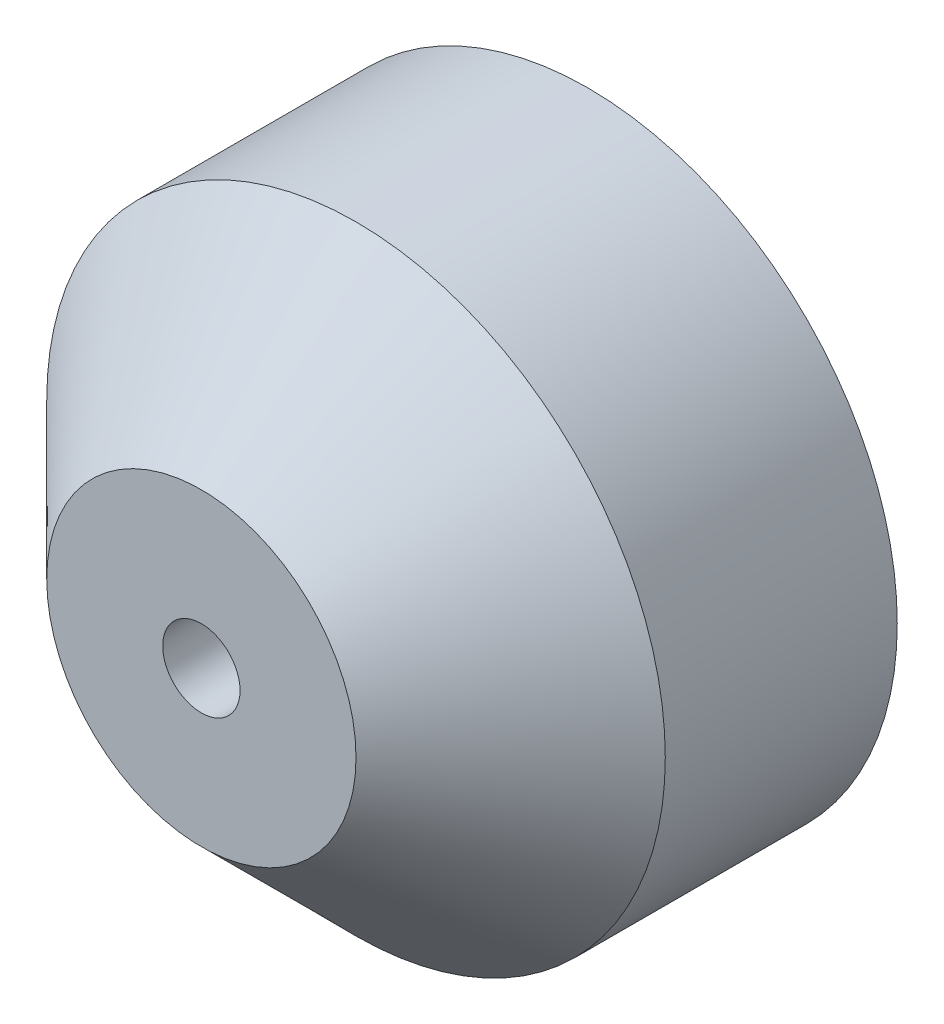
SolidWorks part; units mm, degrees
ref_plane "Front Plane" through (0, 0, 0) normal (0, 0, 1) x (1, 0, 0)
ref_plane "Top Plane" through (0, 0, 0) normal (0, 1, 0) x (1, 0, 0)
ref_plane "Right Plane" through (0, 0, 0) normal (1, 0, 0) x (0, 0, -1)
sketch "Sketch1" plane through (0, 0, 0) normal (0, 0, 1) x (1, 0, 0)
  circle A0 centre (0, 0) radius 20
  dimension "D1" = 40
extrude "Boss-Extrude1" add sketch "Sketch1" along normal blind 25
chamfer "Chamfer1" distance 10 angle 45 1 edges at (20, 0, 25)
sketch "Sketch2" plane through (0, 0, 25) normal (0, 0, 1) x (1, 0, 0)
  circle A0 centre (0, 0) radius 2.5
  dimension "D1" = 5
extrude "Cut-Extrude1" cut sketch "Sketch2" against normal blind 15
sketch "Sketch3" plane through (0, 0, 0) normal (0, 0, -1) x (-1, 0, 0)
  circle A0 centre (0, 0) radius 7.5
  dimension "D1" = 15
extrude "Boss-Extrude2" add sketch "Sketch3" along normal blind 7
